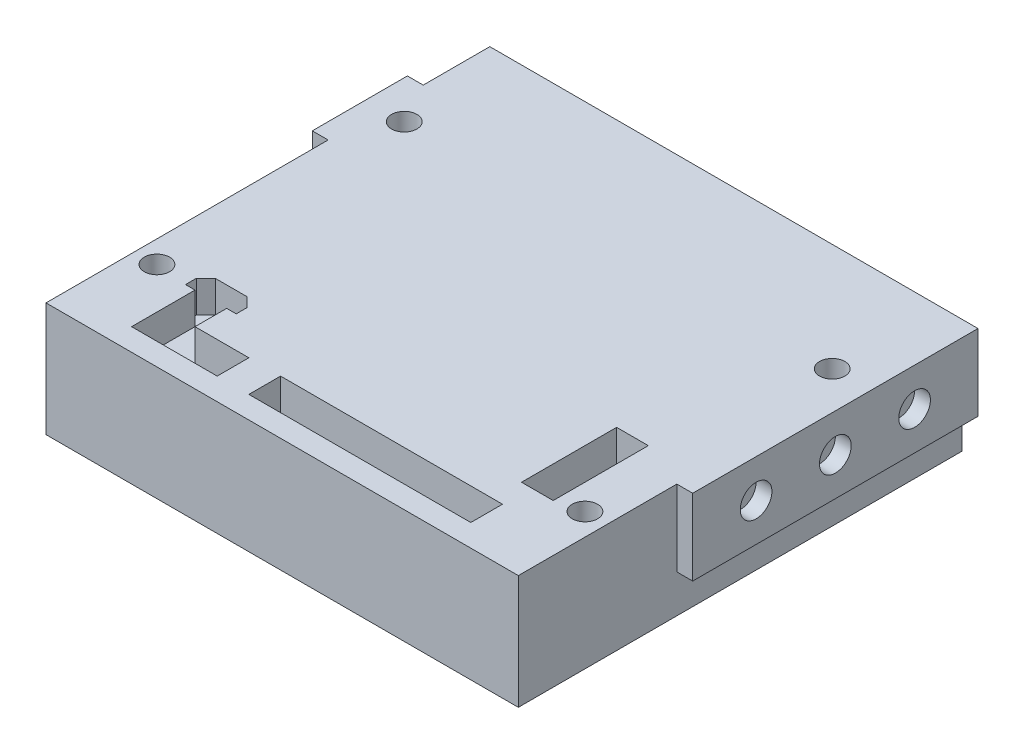
SolidWorks part; units mm, degrees
material "201.0-T6 Insulated Mold Casting (SS)"
ref_plane "Front Plane" through (0, 0, 0) normal (0, 0, 1) x (1, 0, 0)
ref_plane "Top Plane" through (0, 0, 0) normal (0, 1, 0) x (1, 0, 0)
ref_plane "Right Plane" through (0, 0, 0) normal (1, 0, 0) x (0, 0, -1)
sketch "Sketch1" plane through (0, 0, 0) normal (0, 1, 0) x (1, 0, 0)
  line L1 (-37.25, -35) -> (37.25, -35)
  line L2 (-37.25, -35) -> (-37.25, 35)
  line L3 (-37.25, 35) -> (37.25, 35)
  line L4 (37.25, -35) -> (37.25, 35)
  line L5 (-37.25, -35) -> (37.25, 35) construction
  line L6 (-37.25, 35) -> (37.25, -35) construction
  point P0 (0, 0)
  dimension "D1" = 74.5
  dimension "D2" = 70
extrude "Boss-Extrude1" add sketch "Sketch1" along normal blind 18
sketch "Sketch3" plane through (0, 18, 0) normal (0, 1, 0) x (1, 0, 0)
  line L0 (37.25, -35) -> (37.25, 35) construction
  line L1 (-27.25, -21.5) -> (-22.25, -21.5)
  line L2 (-27.25, -21.5) -> (-27.25, -31.5)
  line L3 (-27.25, -31.5) -> (-22.25, -31.5)
  line L4 (-22.25, -21.5) -> (-22.25, -31.5)
  line L5 (-27.25, -21.5) -> (-22.25, -31.5) construction
  line L6 (-27.25, -31.5) -> (-22.25, -21.5) construction
  line L7 (-22.25, -26.5) -> (-13.75, -26.5)
  line L8 (-22.25, -26.5) -> (-22.25, -31.5)
  line L9 (-22.25, -31.5) -> (-13.75, -31.5)
  line L10 (-13.75, -26.5) -> (-13.75, -31.5)
  line L11 (-22.25, -26.5) -> (-13.75, -31.5) construction
  line L12 (-22.25, -31.5) -> (-13.75, -26.5) construction
  line L13 (-8.75, -31.5) -> (9.75, -31.5)
  line L14 (-8.75, -31.5) -> (-8.75, -26.5)
  line L15 (-8.75, -26.5) -> (9.75, -26.5)
  line L16 (9.75, -31.5) -> (9.75, -26.5)
  line L17 (-8.75, -31.5) -> (9.75, -26.5) construction
  line L18 (-8.75, -26.5) -> (9.75, -31.5) construction
  line L19 (9.75, -26.5) -> (26.25, -26.5)
  line L20 (9.75, -26.5) -> (9.75, -31.5)
  line L21 (9.75, -31.5) -> (26.25, -31.5)
  line L22 (26.25, -26.5) -> (26.25, -31.5)
  line L23 (9.75, -26.5) -> (26.25, -31.5) construction
  line L24 (9.75, -31.5) -> (26.25, -26.5) construction
  line L25 (24.75, -7) -> (29.75, -7)
  line L26 (24.75, -7) -> (24.75, -22)
  line L27 (24.75, -22) -> (29.75, -22)
  line L28 (29.75, -7) -> (29.75, -22)
  line L29 (24.75, -7) -> (29.75, -22) construction
  line L30 (24.75, -22) -> (29.75, -7) construction
  line L31 (-37.25, -35) -> (37.25, -35) construction
  line L32 (-28.75, -21.5) -> (-20.75, -21.5)
  line L33 (-20.75, -21.5) -> (-20.75, -19.8)
  line L34 (-20.75, -19.8) -> (-22.25, -18.3)
  line L35 (-22.25, -18.3) -> (-27.25, -18.3)
  line L36 (-27.25, -18.3) -> (-28.75, -19.8)
  line L37 (-28.75, -19.8) -> (-28.75, -21.5)
  point P0 (-24.75, -26.5)
  point P5 (-18, -29)
  point P10 (0.5, -29)
  point P15 (18, -29)
  point P20 (27.25, -14.5)
  point P37 (-24.75, -21.5)
  point P38 (-24.75, -21.5)
  dimension "D1" = 5
  dimension "D2" = 10
  dimension "D3" = 13.5
  dimension "D4" = 18.5
  dimension "D5" = 35
  dimension "D6" = 5
  dimension "D7" = 11
  dimension "D8" = 7.5
  dimension "D9" = 4.5
  dimension "D10" = 15
  dimension "D11" = 3.5
  dimension "D12" = 5
  dimension "D13" = 5
  dimension "D14" = 3.2
  dimension "D15" = 8
  dimension "D16" = 1.5
extrude "Cut-Extrude1" cut sketch "Sketch3" against normal blind 5 contours L4 L1 L2 L3 | L10 L7 L4 L9 | L36 L37 L32 L1 L33 L34 L35 | L13 L16 L15 L14 | L22 L19 L16 L21 | L28 L25 L26 L27
sketch "Sketch4" plane through (37.25, 0, 0) normal (1, 0, 0) x (0, 0, -1)
  line L0 (35, 18) -> (35, 0) construction
  line L2 (-10, 6) -> (35, 6)
  line L3 (-10, 6) -> (-10, 18)
  line L4 (-10, 18) -> (35, 18)
  line L5 (35, 6) -> (35, 18)
  line L6 (-10, 6) -> (35, 18) construction
  line L7 (-10, 18) -> (35, 6) construction
  circle A0 centre (25, 12) radius 2.5
  circle A1 centre (12.5, 12) radius 2.5
  circle A2 centre (0, 12) radius 2.5
  point P10 (12.5, 12)
  dimension "D1" = 5
  dimension "D2" = 10
  dimension "D3" = 12.5
  dimension "D4" = 12.5
  dimension "D5" = 6
  dimension "D6" = 12
  dimension "D7" = 45
extrude "Boss-Extrude2" add sketch "Sketch4" along normal blind 2.5
sketch "Sketch5" plane through (-37.25, 0, 0) normal (-1, 0, 0) x (0, 0, 1)
  line L0 (-35, 0) -> (35, 0) construction
  line L1 (-24.5, 18) -> (-9.5, 18)
  line L2 (-24.5, 18) -> (-24.5, 0)
  line L3 (-24.5, 0) -> (-9.5, 0)
  line L4 (-9.5, 18) -> (-9.5, 0)
  line L5 (-24.5, 18) -> (-9.5, 0) construction
  line L6 (-24.5, 0) -> (-9.5, 18) construction
  line L7 (-35, 18) -> (35, 18) construction
  line L8 (-35, 18) -> (-35, 0) construction
  line L9 (-17, 12) -> (-17, 6) construction
  line L10 (-17, 12) -> (-17, 18) construction
  line L11 (-17, 6) -> (-17, 0) construction
  circle A0 centre (-17, 12) radius 2.5
  circle A1 centre (-17, 6) radius 2.5
  point P0 (-17, 9)
  point P13 (-17, 9)
  point P16 (-24.5, 9)
  dimension "D1" = 5
  dimension "D2" = 18
  dimension "D3" = 15
extrude "Boss-Extrude3" add sketch "Sketch5" along normal blind 2.5
sketch "Sketch6" plane through (0, 0, 0) normal (0, -1, 0) x (1, 0, 0)
  line L0 (-37.25, -9.5) -> (-37.25, 35) construction
  line L3 (37.25, -35) -> (-37.25, -35) construction
  circle A0 centre (-33.75, 21) radius 2
  circle A1 centre (-33.75, -18) radius 2
  point P8 (-47.6922, -29.7022)
  dimension "D1" = 4
  dimension "D2" = 3.5
  dimension "D3" = 39
  dimension "D4" = 17
extrude "Cut-Extrude2" cut sketch "Sketch6" against normal through all
mirror "Mirror1" about plane through (0, 0, 0) normal (1, 0, 0) of "Cut-Extrude2"
